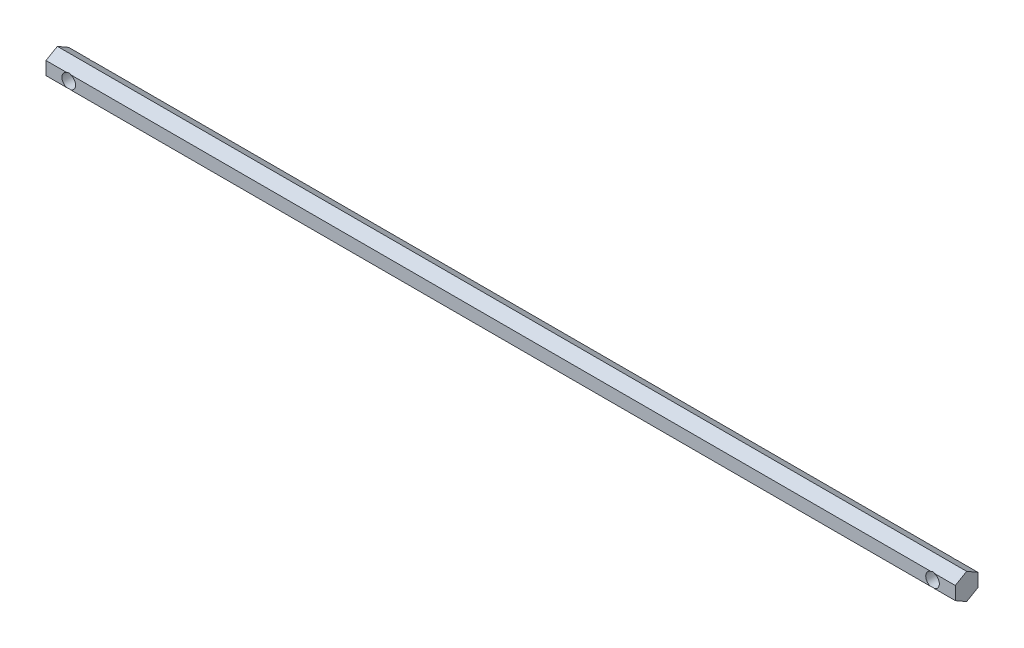
SolidWorks part; units mm, degrees
ref_plane "Plano frontal" through (0, 0, 0) normal (0, 0, 1) x (1, 0, 0)
ref_plane "Plano superior" through (0, 0, 0) normal (0, 1, 0) x (1, 0, 0)
ref_plane "Plano direito" through (0, 0, 0) normal (1, 0, 0) x (0, 0, -1)
sketch "Sketch1" plane through (0, 0, 0) normal (1, 0, 0) x (0, 0, -1)
  line L0 (-8.3414, 2.8868) -> (9.6861, 2.8868) construction
  line L1 (0, 5.7735) -> (-5, 2.8868)
  line L2 (-5, 2.8868) -> (-5, -2.8868)
  line L3 (-5, -2.8868) -> (0, -5.7735)
  line L4 (0, -5.7735) -> (5, -2.8868)
  line L5 (5, -2.8868) -> (5, 2.8868)
  line L6 (5, 2.8868) -> (0, 5.7735)
  line L7 (-8.3414, -2.8868) -> (9.6861, -2.8868) construction
  circle A0 centre (0, 0) radius 5 construction
  dimension "D1" = 10
extrude "Boss-Extrude1" add sketch "Sketch1" along normal mid plane 400
sketch "Sketch2" plane through (0, 0, 0) normal (0, 0, 1) x (1, 0, 0)
  line L0 (120.1463, 0) -> (-122.4896, 0) construction
  line L1 (0, 39.7277) -> (0, -43.0342) construction
  circle A0 centre (190, 0) radius 3
  circle A1 centre (-190, 0) radius 3
  dimension "D3" = 6
  dimension "D4" = 6
  dimension "D1" = 190
  dimension "D2" = 190
extrude "Cut-Extrude1" cut sketch "Sketch2" against normal through all both and the other way through all
